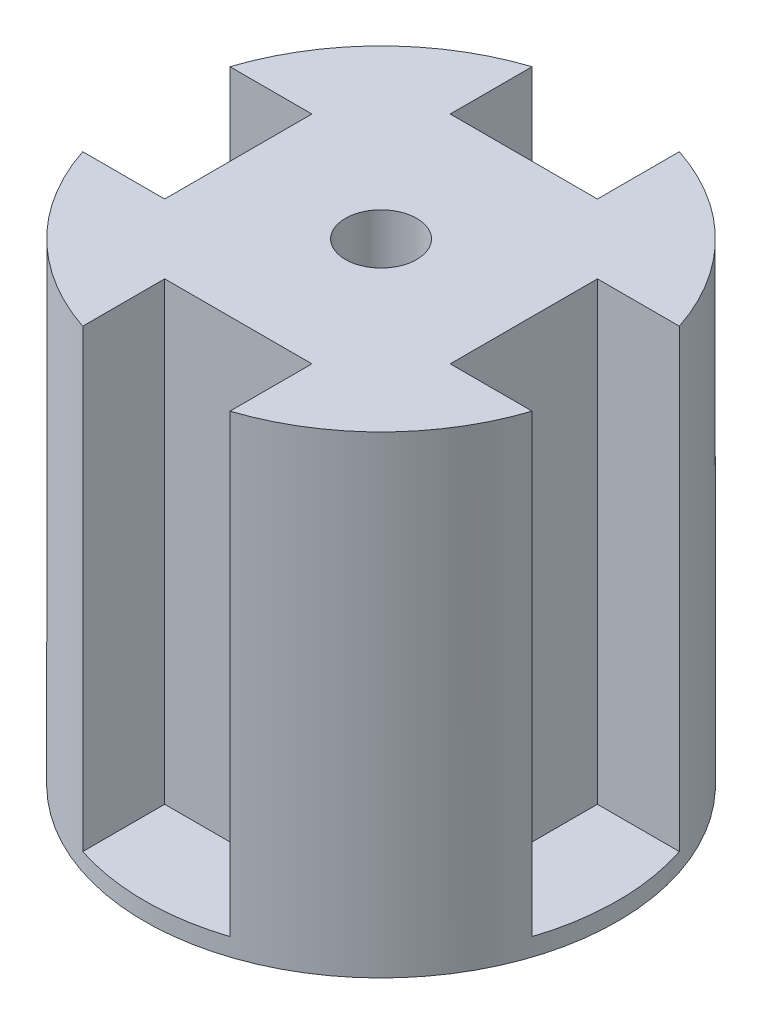
SolidWorks part; units mm, degrees
ref_plane "前视基准面" through (0, 0, 0) normal (0, 0, 1) x (1, 0, 0)
ref_plane "上视基准面" through (0, 0, 0) normal (0, 1, 0) x (1, 0, 0)
ref_plane "右视基准面" through (0, 0, 0) normal (1, 0, 0) x (0, 0, -1)
sketch "Sketch1" plane through (0, 0, 0) normal (0, 1, 0) x (1, 0, 0)
  line L0 (-8, 16) -> (8, 16) construction
  line L1 (25, -8) -> (-25, -8) construction
  line L2 (25, -8) -> (25, 8) construction
  line L3 (25, 8) -> (-25, 8) construction
  line L4 (-25, -8) -> (-25, 8) construction
  line L5 (25, -8) -> (-25, 8) construction
  line L6 (25, 8) -> (-25, -8) construction
  line L7 (8, -25) -> (-8, -25) construction
  line L8 (8, -25) -> (8, 25) construction
  line L9 (8, 25) -> (-8, 25) construction
  line L10 (-8, -25) -> (-8, 25) construction
  line L11 (8, -25) -> (-8, 25) construction
  line L12 (8, 25) -> (-8, -25) construction
  line L13 (16, 8) -> (16, -8) construction
  line L14 (8, -16) -> (-8, -16) construction
  line L15 (-16, -8) -> (-16, 8) construction
  circle A0 centre (0, 0) radius 26.2488 construction
  point P0 (0, 0)
  point P6 (0, 0)
  point P22 (0, 0)
  dimension "D1" = 16
  dimension "D2" = 16
  dimension "D3" = 50
  dimension "D4" = 50
  dimension "D6" = 9
  dimension "D5" = 4
sketch "Sketch2" plane through (0, 0, 0) normal (0, 1, 0) x (1, 0, 0)
  line L0 (25, -8) -> (-25, 8) construction
  line L1 (0, 0) -> (0, 26.5) construction
  line L2 (-8.25, 25.1831) -> (-8.25, 16)
  line L3 (-8.25, 16) -> (8.25, 16)
  line L4 (-8, 16) -> (8, 16) construction
  line L5 (8.25, 25.1831) -> (8.25, 16)
  line L6 (-8, -25) -> (-8, 25) construction
  line L7 (25.1831, 8.25) -> (16, 8.25)
  line L8 (16, 8.25) -> (16, -8.25)
  line L9 (25.1831, -8.25) -> (16, -8.25)
  line L10 (8.25, -25.1831) -> (8.25, -16)
  line L11 (8.25, -16) -> (-8.25, -16)
  line L12 (-8.25, -25.1831) -> (-8.25, -16)
  line L13 (-25.1831, -8.25) -> (-16, -8.25)
  line L14 (-16, -8.25) -> (-16, 8.25)
  line L15 (-25.1831, 8.25) -> (-16, 8.25)
  arc A0 (-8.25, 25.1831) -> (-25.1831, 8.25) centre (0, 0) ccw
  arc A1 (25.1831, 8.25) -> (8.25, 25.1831) centre (0, 0) ccw
  arc A2 (-25.1831, -8.25) -> (-8.25, -25.1831) centre (0, 0) ccw
  arc A3 (8.25, -25.1831) -> (25.1831, -8.25) centre (0, 0) ccw
  point P11 (0, 16)
  point P31 (0, 0)
  dimension "D3" = 53
  dimension "D1" = 0.25
  dimension "D2" = 4
extrude "Boss-Extrude1" add sketch "Sketch2" along normal blind 51
sketch "Sketch3" plane through (0, 0, 0) normal (0, -1, 0) x (1, 0, 0)
  circle A0 centre (0, 0) radius 26.5
extrude "Boss-Extrude2" add sketch "Sketch3" along normal blind 2
sketch "Sketch4" plane through (0, 51, 0) normal (0, 1, 0) x (1, 0, 0)
  circle A0 centre (0, 0) radius 4
  dimension "D1" = 8
extrude "Cut-Extrude1" cut sketch "Sketch4" against normal through all
